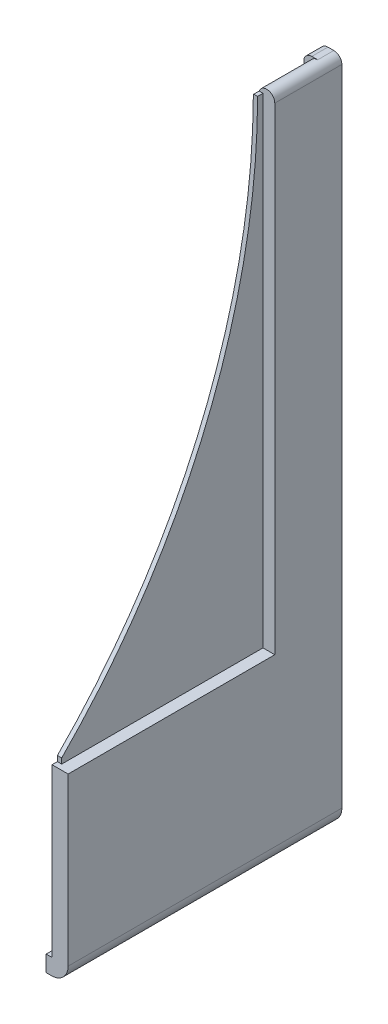
SolidWorks part; units mm, degrees
ref_plane "Front Plane" through (0, 0, 0) normal (0, 0, 1) x (1, 0, 0)
ref_plane "Top Plane" through (0, 0, 0) normal (0, 1, 0) x (1, 0, 0)
ref_plane "Right Plane" through (0, 0, 0) normal (1, 0, 0) x (0, 0, -1)
sketch "Croquis1" plane through (0, 0, 0) normal (0, 0, 1) x (1, 0, 0)
  line L0 (0, 0) -> (1, 0)
  line L1 (1.1, 0.1) -> (1.1, 120.1)
  line L2 (0, -3) -> (1, -3)
  line L3 (4.1, 0.1) -> (4.1, 120.1)
  line L4 (1, 0) -> (1, -3)
  line L5 (1.1, 0.1) -> (4.1, 0.1)
  line L6 (0, -3) -> (0, 0)
  arc A0 (1, 0) -> (1.1, 0.1) centre (1, 0.1) ccw
  arc A1 (1, -3) -> (4.1, 0.1) centre (1, 0.1) ccw
  arc A2 (1.1, 120.1) -> (4.1, 120.1) centre (2.6, 120.1) cw
  dimension "D1" = 0.1
  dimension "D3" = 90
  dimension "D4" = 120
  dimension "D5" = 1
  dimension "D2" = 3
extrude "Saliente-Extruir1" add sketch "Croquis1" along normal blind 48 contours A2 L1 L5 L3 | L4 A1 L5 A0 | L0 L6 L2 L4
sketch "Croquis2" plane through (0, 0, 0) normal (0, 0, -1) x (-1, 0, 0)
  line L0 (0, -3) -> (0, 120.1)
  line L1 (-1.5, 121.6) -> (-2.6, 121.6)
  line L2 (-4.1, 0.1) -> (-4.1, 120.1) construction
  line L3 (0, -3) -> (-1, -3) construction
  line L4 (-4.1, 0.1) -> (-4.1, 120.1)
  line L5 (0, -3) -> (-1, -3)
  arc A1 (-1.1, 120.1) -> (-4.1, 120.1) centre (-2.6, 120.1) ccw construction
  arc A2 (0, 120.1) -> (-1.5, 121.6) centre (-1.5, 120.1) ccw
  arc A3 (-4.1, 0.1) -> (-1, -3) centre (-1, 0.1) ccw construction
  arc A4 (-1.1, 120.1) -> (-4.1, 120.1) centre (-2.6, 120.1) ccw
  arc A5 (-4.1, 0.1) -> (-1, -3) centre (-1, 0.1) ccw
  arc M1 (-1.1, 120.1) -> (-4.1, 120.1) centre (-2.6, 120.1) ccw
  line M2 (-4.1, 120.1) -> (-4.1, 0.1)
  arc M3 (-4.1, 0.1) -> (-1, -3) centre (-1, 0.1) ccw
  line M4 (-1, -3) -> (0, -3)
  line M5 (0, -3) -> (0, 0)
  line M6 (0, 0) -> (-1, 0)
  arc M7 (-1, 0) -> (-1.1, 0.1) centre (-1, 0.1) cw
  line M8 (-1.1, 0.1) -> (-1.1, 120.1)
  dimension "D1" = 1.5
extrude "Saliente-Extruir2" add sketch "Croquis2" along normal blind 3 contours L0 A2 L1 M1 M8 M7 M6 M5 | M8 M1 M2 M3 M4 M5 M6 M7
sketch "Croquis3" plane through (4.1, 0, 0) normal (1, 0, 0) x (0, 0, -1)
  line L1 (-48, 121.6) -> (-9.5, 121.6)
  line L2 (-48, 121.6) -> (-48, 31.1)
  line L3 (-48, 31.1) -> (-9.5, 31.1)
  line L4 (-9.5, 121.6) -> (-9.5, 31.1)
  dimension "D1" = 90.5
  dimension "D2" = 38.5
extrude "Cortar-Extruir1" cut sketch "Croquis3" against normal offset from surface (2.2 mm away) 0.8 up to face at (1.1, 60.1, 24)
sketch "Croquis4" plane through (1.9, 0, 0) normal (1, 0, 0) x (0, 0, -1)
  line L0 (-9.5, 121.6) -> (-9.5, 120.6)
  line L1 (-9.5, 31.1) -> (-9.5, 121.4266) construction
  line L2 (-9.5, 120.6) -> (-10.5, 120.6)
  line L3 (-48, 31.1) -> (-47, 31.1)
  line L4 (-48, 31.1) -> (-9.5, 31.1) construction
  line L5 (-47, 31.1) -> (-47, 32.1)
  line L6 (-10.5, 120.6) -> (-10.5, 123.8175) construction
  line L7 (-9.5, 121.4266) -> (-48, 121.4266) construction
  line L8 (-48, 121.4266) -> (-48, 31.1) construction
  line L9 (-9.5, 121.4266) -> (-48, 121.4266)
  line L10 (-48, 121.4266) -> (-48, 31.1)
  arc A0 (-10.5, 120.6) -> (-47, 32.1) centre (-136.0411, 120.6) cw
  line M1 (-9.5, 121.4266) -> (-48, 121.4266)
  line M2 (-48, 121.4266) -> (-48, 31.1)
  line M3 (-48, 31.1) -> (-9.5, 31.1)
  line M4 (-9.5, 31.1) -> (-9.5, 121.4266)
  dimension "D1" = 1
  dimension "D2" = 1
  dimension "D3" = 1
  dimension "D4" = 1
extrude "Cortar-Extruir2" cut sketch "Croquis4" against normal through all contours A0 L6 L9 L5 M2 M3 | L6 L2 M4 M1
